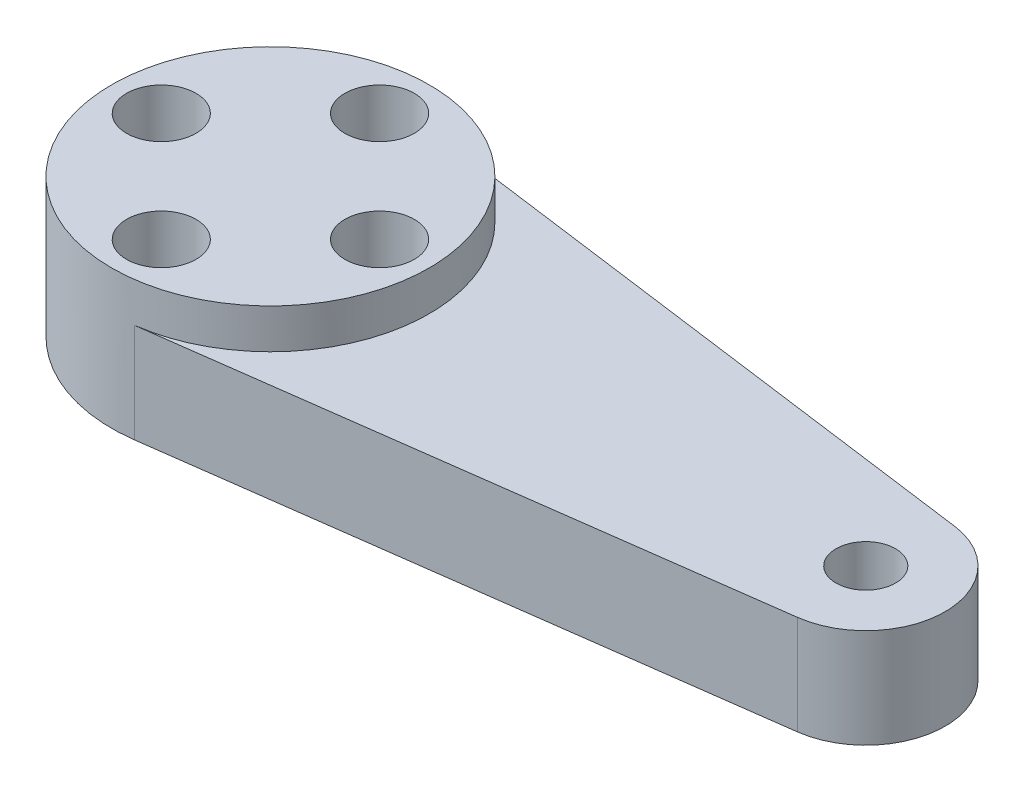
SolidWorks part; units mm, degrees
ref_plane "Front Plane" through (0, 0, 0) normal (0, 0, 1) x (1, 0, 0)
ref_plane "Top Plane" through (0, 0, 0) normal (0, 1, 0) x (1, 0, 0)
ref_plane "Right Plane" through (0, 0, 0) normal (1, 0, 0) x (0, 0, -1)
sketch "Sketch1" plane through (0, 0, 0) normal (0, 1, 0) x (1, 0, 0)
  line L0 (1.0667, 7.9286) -> (30.5333, 3.9643)
  line L1 (1.0667, -7.9286) -> (30.5333, -3.9643)
  arc A0 (1.0667, 7.9286) -> (1.0667, -7.9286) centre (0, 0) ccw
  circle A1 centre (30, 0) radius 1.5
  arc A2 (30.5333, -3.9643) -> (30.5333, 3.9643) centre (30, 0) ccw
  circle A3 centre (-5.5, 0) radius 1.75
  circle A4 centre (0, 5.5) radius 1.75
  circle A5 centre (5.5, 0) radius 1.75
  circle A6 centre (0, -5.5) radius 1.75
  point P19 (0, 0)
  dimension "D1" = 16
  dimension "D3" = 3
  dimension "D4" = 8
  dimension "D6" = 3.5
  dimension "D2" = 30
  dimension "D5" = 5.5
  dimension "D7" = 4
extrude "Boss-Extrude1" add sketch "Sketch1" along normal blind 5
sketch "Sketch2" plane through (0, 5, 0) normal (0, 1, 0) x (1, 0, 0)
  circle A0 centre (0, 0) radius 8
  circle A1 centre (-5.5, 0) radius 1.75 construction
  circle A2 centre (0, -5.5) radius 1.75 construction
  circle A3 centre (5.5, 0) radius 1.75 construction
  circle A4 centre (0, 5.5) radius 1.75 construction
  circle A5 centre (-5.5, 0) radius 1.75
  circle A6 centre (0, -5.5) radius 1.75
  circle A7 centre (5.5, 0) radius 1.75
  circle A8 centre (0, 5.5) radius 1.75
extrude "Boss-Extrude2" add sketch "Sketch2" along normal blind 2
